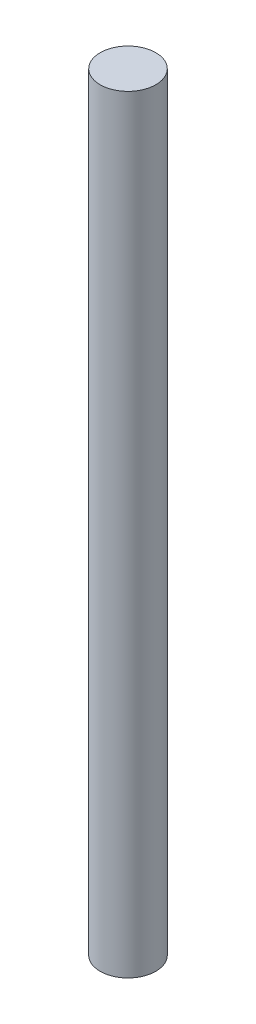
SolidWorks part; units mm, degrees
material "Beech"
ref_plane "Front Plane" through (0, 0, 0) normal (0, 0, 1) x (1, 0, 0)
ref_plane "Top Plane" through (0, 0, 0) normal (0, 1, 0) x (1, 0, 0)
ref_plane "Right Plane" through (0, 0, 0) normal (1, 0, 0) x (0, 0, -1)
sketch "Sketch1" plane through (0, 0, 0) normal (0, 1, 0) x (1, 0, 0)
  circle A0 centre (0, 0) radius 8
  dimension "D1" = 16
extrude "Boss-Extrude1" add sketch "Sketch1" along normal blind 221
